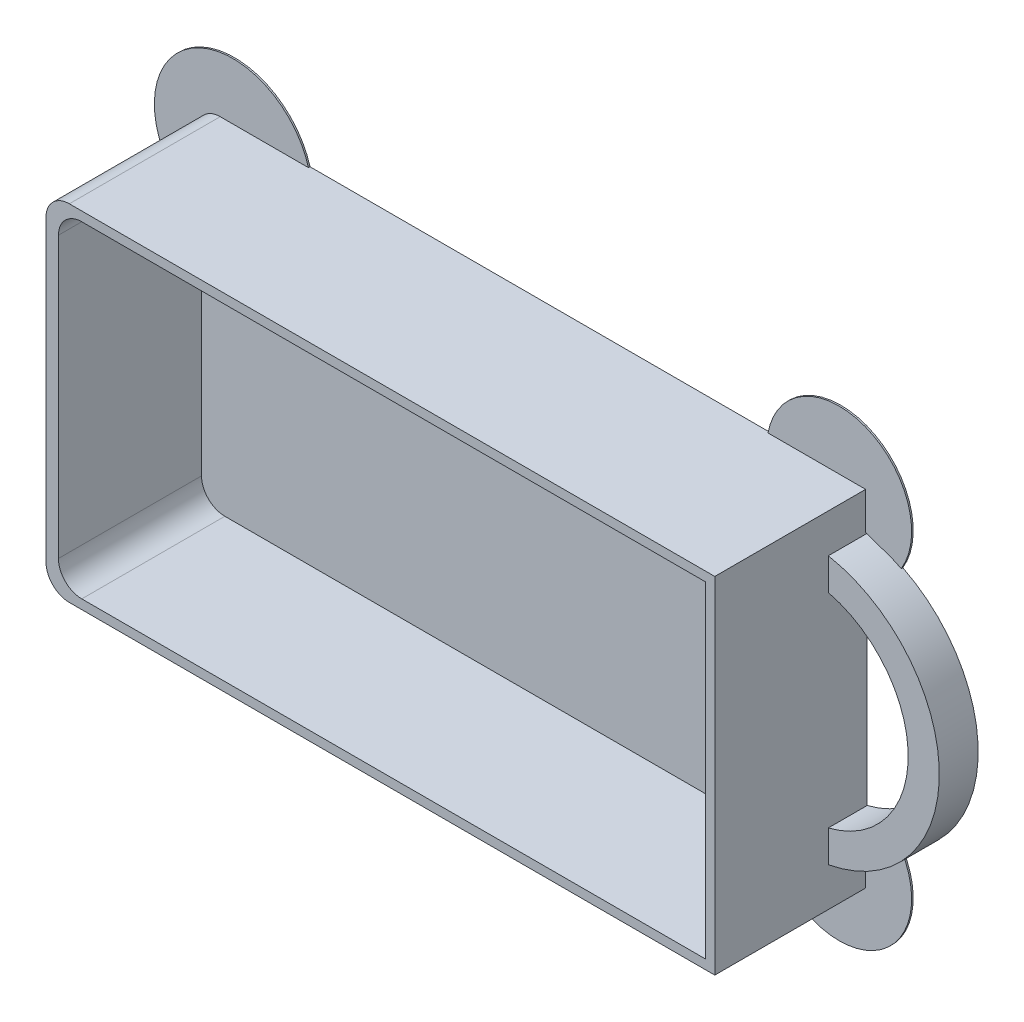
SolidWorks part; units mm, degrees
ref_plane "Спереди" through (0, 0, 0) normal (0, 0, 1) x (1, 0, 0)
ref_plane "Сверху" through (0, 0, 0) normal (0, 1, 0) x (1, 0, 0)
ref_plane "Справа" through (0, 0, 0) normal (1, 0, 0) x (0, 0, -1)
other "Configuration Table"
sketch "Эскиз1" plane through (0, 0, 0) normal (0, 0, 1) x (1, 0, 0)
  line L1 (-43, 22.2) -> (43, 22.2)
  line L2 (-43, 22.2) -> (-43, -22.2)
  line L3 (-43, -22.2) -> (43, -22.2)
  line L4 (43, 22.2) -> (43, -22.2)
  line L5 (-43, 22.2) -> (43, -22.2) construction
  line L6 (-43, -22.2) -> (43, 22.2) construction
  point P0 (0, 0)
  dimension "D1" = 86
  dimension "D2" = 44.4
extrude "Бобышка-Вытянуть1" add sketch "Эскиз1" along normal blind 19.6
sketch "Эскиз2" plane through (0, 0, 0) normal (0, 0, 1) x (1, 0, 0)
  line L0 (0, 0) -> (43, 0) construction
  line L1 (43, -22.2) -> (43, 22.2) construction
  line L2 (43, 17.2) -> (43, 13.1088)
  line L3 (43, -17.2) -> (43, -13.1088)
  arc A0 (43, -17.2) -> (43, 17.2) centre (39.7735, 0) ccw
  arc A1 (43, -13.1088) -> (43, 13.1088) centre (39.7735, 0) ccw
  dimension "D3" = 13.5
  dimension "D4" = 4
  dimension "D1" = 5
  dimension "D2" = 5
extrude "Бобышка-Вытянуть2" add sketch "Эскиз2" along normal blind 5
sketch "Эскиз3" plane through (0, 0, 19.6) normal (0, 0, 1) x (1, 0, 0)
  line L5 (-41.4, 22.2) -> (-41.4, -22.2)
  line L6 (-43, -21) -> (41.8, -21)
  line L7 (41.8, -21) -> (41.8, 21)
  line L8 (41.8, 21) -> (-43, 21)
  line L9 (-41.4, -21) -> (41.8, -21)
  line L10 (41.8, -21) -> (41.8, 21)
  line L11 (41.8, 21) -> (-41.4, 21)
  line L12 (-41.4, 21) -> (-41.4, -21)
  dimension "D1" = 1.2
  dimension "D2" = 1.6
extrude "Вырез-Вытянуть1" cut sketch "Эскиз3" against normal offset from surface (18.4 mm away) 1.2 up to face at (48.1368, 0, 0)
fillet "Скругление1" radius 3 4 edges at (-43, 22.2, 9.8) (-43, -22.2, 9.8) (-41.4, -21, 10.4) (-41.4, 21, 10.4)
sketch "Эскиз4" plane through (0, 0, 0) normal (0, 0, -1) x (-1, 0, 0)
  line L0 (-43, 22.2) -> (42.1213, -21.3213) construction
  line L1 (-43, -22.2) -> (42.1213, 21.3213) construction
  line L2 (-43, 22.2) -> (40, 22.2) construction
  line L3 (0, 0) -> (-25.3008, 0) construction
  line L4 (0, 0) -> (0, 12.8607) construction
  line L5 (-47.5829, 15.6609) -> (-30.4455, 22.2)
  line L6 (-47.5829, -15.6609) -> (-30.4455, -22.2)
  line L7 (43, 19.2) -> (43, -19.2) construction
  line L8 (43, 10.4177) -> (28.646, 22.2)
  line L9 (43, -10.4177) -> (28.646, -22.2)
  arc A0 (40, -22.2) -> (43, -19.2) centre (40, -19.2) ccw construction
  arc A1 (43, 19.2) -> (40, 22.2) centre (40, 19.2) ccw construction
  arc A2 (-30.4455, 22.2) -> (-47.5829, 15.6609) centre (-39.598, 20.4606) ccw
  arc A3 (-43, 17.2) -> (-43, -17.2) centre (-39.7735, 0) ccw construction
  arc A4 (-30.4455, -22.2) -> (-47.5829, -15.6609) centre (-39.598, -20.4606) cw
  arc A5 (28.646, 22.2) -> (43, 10.4177) centre (38.3581, 19.3972) cw
  arc A6 (28.646, -22.2) -> (43, -10.4177) centre (38.3581, -19.3972) ccw
extrude "Бобышка-Вытянуть3" add sketch "Эскиз4" against normal blind 0.2
